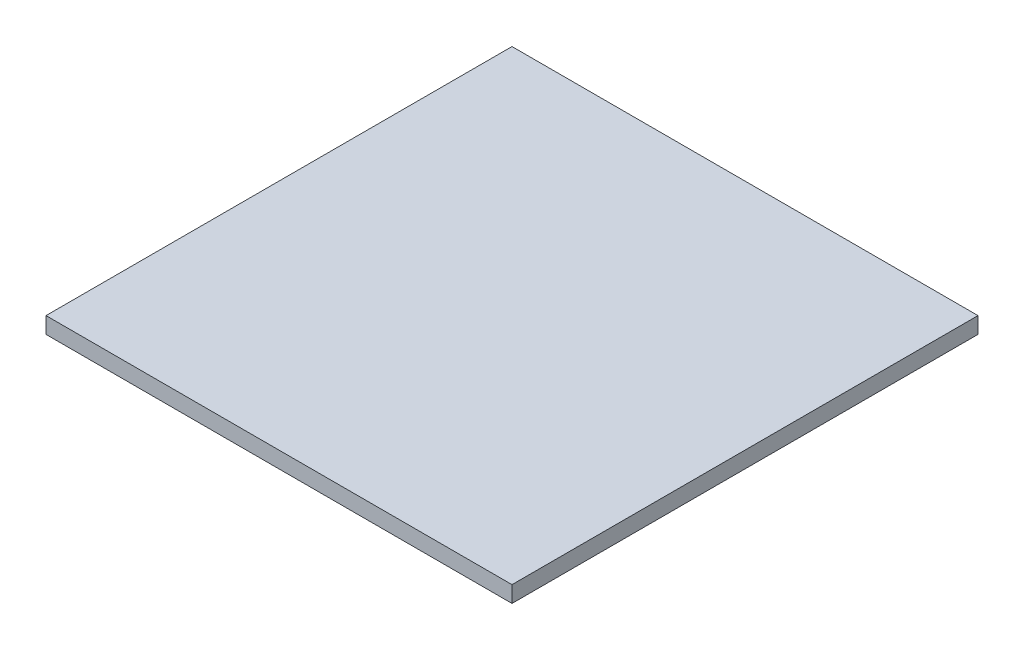
SolidWorks part; units mm, degrees
material "Cast Alloy Steel"
ref_plane "Front Plane" through (0, 0, 0) normal (0, 0, 1) x (1, 0, 0)
ref_plane "Top Plane" through (0, 0, 0) normal (0, 1, 0) x (1, 0, 0)
ref_plane "Right Plane" through (0, 0, 0) normal (1, 0, 0) x (0, 0, -1)
sketch "Sketch1" plane through (0, 0, 0) normal (0, 1, 0) x (1, 0, 0)
  line L1 (0, 0) -> (100, 0)
  line L2 (0, 0) -> (0, 100)
  line L3 (0, 100) -> (100, 100)
  line L4 (100, 0) -> (100, 100)
  dimension "D1" = 100
  dimension "D2" = 100
extrude "Boss-Extrude1" add sketch "Sketch1" along normal blind 3.5
